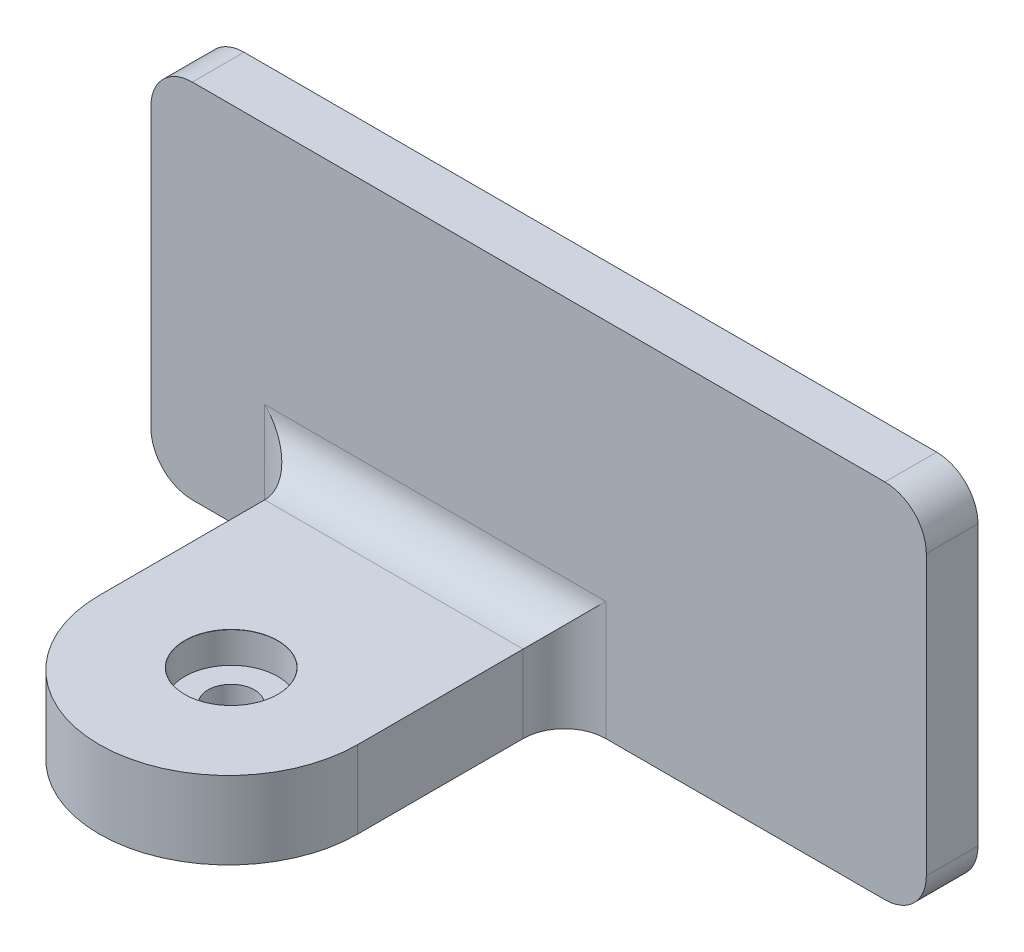
SolidWorks part; units mm, degrees
ref_plane "Front Plane" through (0, 0, 0) normal (0, 0, 1) x (1, 0, 0)
ref_plane "Top Plane" through (0, 0, 0) normal (0, 1, 0) x (1, 0, 0)
ref_plane "Right Plane" through (0, 0, 0) normal (1, 0, 0) x (0, 0, -1)
sketch "Sketch1" plane through (0, 0, 0) normal (0, 0, 1) x (1, 0, 0)
  line L0 (0, 0) -> (0, 70)
  line L1 (0, 70) -> (150, 70)
  line L2 (150, 70) -> (150, 0)
  line L3 (150, 0) -> (0, 0)
  dimension "D1" = 70
  dimension "D2" = 150
extrude "Boss-Extrude1" add sketch "Sketch1" along normal blind 10
sketch "Sketch2" plane through (0, 0, 0) normal (0, -1, 0) x (-1, 0, 0)
  line L0 (-55, -50) -> (-55, 0) construction
  line L1 (0, 0) -> (-150, 0) construction
  line L2 (-80, -50) -> (-80, 0)
  line L3 (-30, -50) -> (-30, 0)
  line L4 (-30, 0) -> (-80, 0)
  arc A0 (-80, -50) -> (-30, -50) centre (-55, -50) ccw
  point P4 (-55, -25)
  dimension "D2" = 25
  dimension "D1" = 30
  dimension "D3" = 50
extrude "Boss-Extrude2" add sketch "Sketch2" against normal blind 15
fillet "Fillet1" radius 8 1 edges at (80, 7.5, 10)
fillet "Fillet2" radius 8 1 edges at (59, 15, 10)
fillet "Fillet3" radius 8 1 edges at (30, 11.5, 10)
fillet "Fillet4" radius 8 1 edges at (150, 70, 5)
fillet "Fillet5" radius 8 1 edges at (150, 0, 5)
fillet "Fillet6" radius 8 1 edges at (0, 70, 5)
fillet "Fillet11" radius 8 1 edges at (0, 0, 5)
hole_wizard "CBORE for M8 Pan Head Machine Screw1" positions "Sketch3" profile "Sketch4" counterbore size "M8" standard "ANSI Metric" end condition through all
sketch "Sketch3" plane through (0, 15, 0) normal (0, 1, 0) x (1, 0, 0)
  point P0 (54.842, -49.3139)
sketch "Sketch4" plane through (54.842, 15, 49.3139) normal (1, 0, 0) x (0, 0, 1)
  line L0 (0, 0) -> (0, 15)
  line L1 (0, 15) -> (4.5, 15)
  line L3 (4.5, 15) -> (4.5, 6)
  line L4 (9, 6) -> (4.5, 6)
  line L5 (9, 6) -> (9, 0.021)
  line L6 (9, 0.021) -> (9.025, 0)
  line L7 (9.025, 0) -> (0, 0)
  line L8 (-9, 0.021) -> (-9.025, 0) construction
  line L11 (0, -6.35) -> (0, 107.95) construction
  dimension "Thru Hole Dia." = 9
  dimension "Thru Hole Depth" = 15
  dimension "C'Bore Dia." = 18
  dimension "C'Bore Depth" = 6
  dimension "Near C'Sink Dia." = 18.05
  dimension "Near C'Sink Angle" = 100
